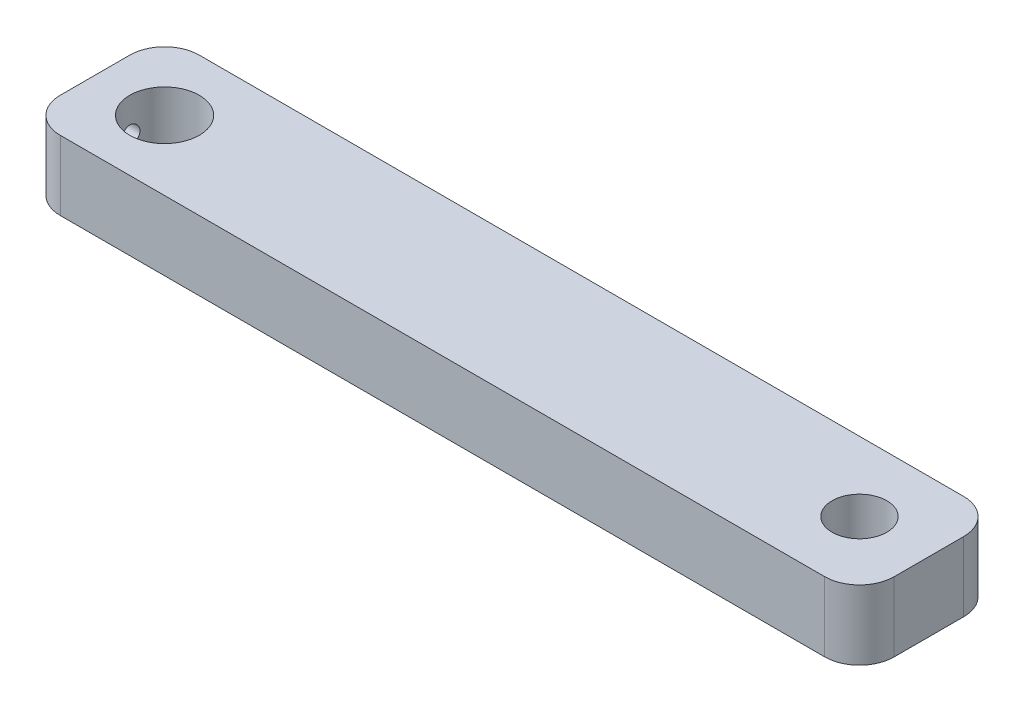
SolidWorks part; units mm, degrees
ref_plane "Front Plane" through (0, 0, 0) normal (0, 0, 1) x (1, 0, 0)
ref_plane "Top Plane" through (0, 0, 0) normal (0, 1, 0) x (1, 0, 0)
ref_plane "Right Plane" through (0, 0, 0) normal (1, 0, 0) x (0, 0, -1)
sketch "Sketch1" plane through (0, 0, 0) normal (0, 1, 0) x (1, 0, 0)
  line L0 (-12.7, 0) -> (0, 0) construction
  line L1 (-12.7, 12.7) -> (139.7, 12.7)
  line L2 (-12.7, 12.7) -> (-12.7, -12.7)
  line L3 (-12.7, -12.7) -> (139.7, -12.7)
  line L4 (139.7, 12.7) -> (139.7, -12.7)
  line L5 (0, 0) -> (127, 0) construction
  circle A0 centre (0, 0) radius 6.35
  circle A1 centre (127, 0) radius 5
  dimension "D1" = 12.7
  dimension "D5" = 10
  dimension "D2" = 25.4
  dimension "D3" = 12.7
  dimension "D4" = 152.4
  dimension "D6" = 12.7
extrude "Boss-Extrude1" add sketch "Sketch1" along normal blind 12.7
fillet "Fillet1" radius 6.35 4 edges at (139.7, 6.35, 12.7) (139.7, 6.35, -12.7) (-12.7, 6.35, 12.7) (-12.7, 6.35, -12.7)
sketch "Sketch2" plane through (-12.7, 0, 0) normal (-1, 0, 0) x (0, 0, 1)
  line L0 (0, 0) -> (0, 12.7) construction
  line L1 (-6.35, 12.7) -> (6.35, 12.7) construction
  point P5 (0, 6.35)
hole_wizard "Tap Drill for M4x0.7 Tap1" positions "Sketch3" profile "Sketch5" hole size "M4x0.7" standard "ANSI Metric"
sketch "Sketch3" plane through (-12.7, 0, 0) normal (-1, 0, 0) x (0, 0, 1)
  point P0 (0, 6.35)
sketch "Sketch5" plane through (-12.7, 6.35, 0) normal (0, 1, 0) x (0, 0, 1)
  line L0 (0, 0) -> (0, 6.35)
  line L1 (0, 6.35) -> (1.65, 6.35)
  line L2 (1.65, 6.35) -> (1.65, 0)
  line L5 (1.65, 0) -> (0, 0)
  line L11 (0, -6.35) -> (0, 107.95) construction
  dimension "Thru Hole Dia." = 3.3
  dimension "Thru Hole Depth" = 6.35
